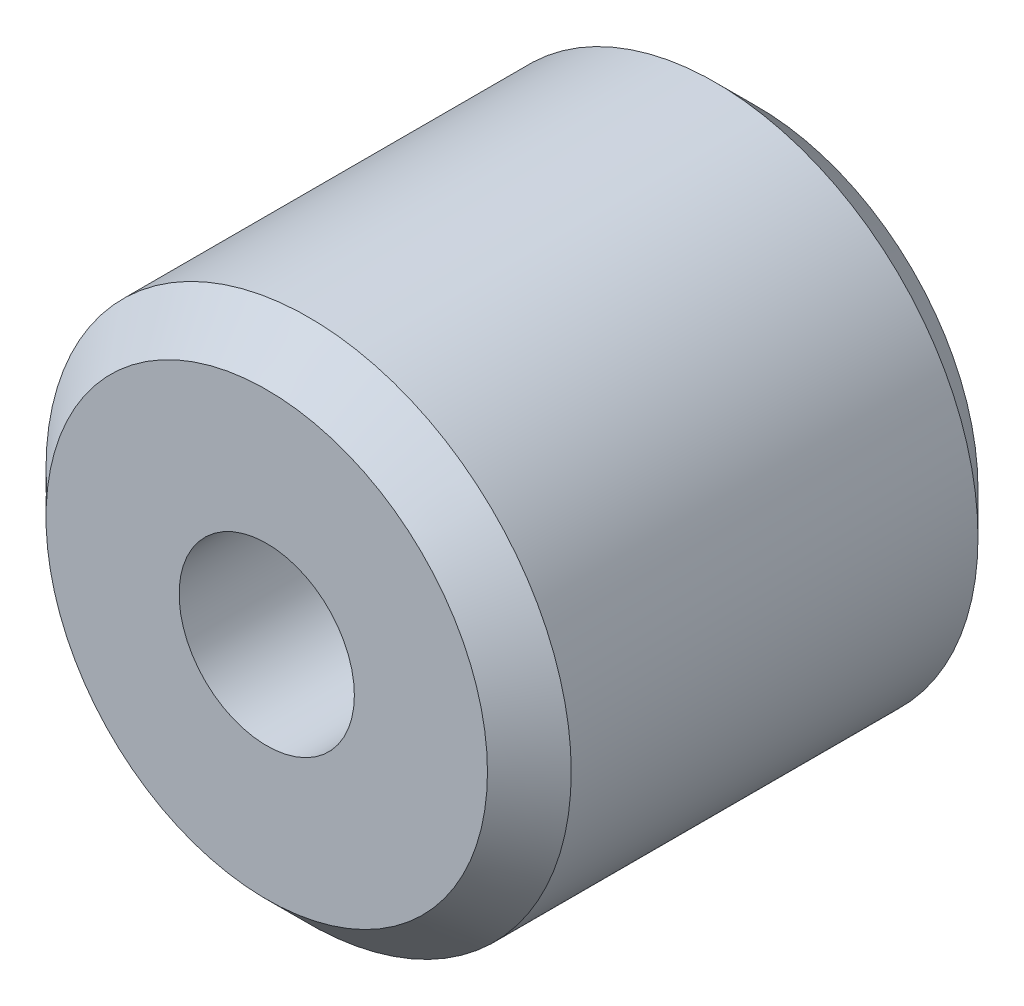
SolidWorks part; units mm, degrees
ref_plane "Front Plane" through (0, 0, 0) normal (0, 0, 1) x (1, 0, 0)
ref_plane "Top Plane" through (0, 0, 0) normal (0, 1, 0) x (1, 0, 0)
ref_plane "Right Plane" through (0, 0, 0) normal (1, 0, 0) x (0, 0, -1)
sketch "Sketch1" plane through (0, 0, 0) normal (1, 0, 0) x (0, 0, -1)
  line L0 (-3.69, 4.765) -> (-4.45, 4.005)
  line L1 (-3.69, 4.765) -> (3.69, 4.765)
  line L3 (4.45, 4.005) -> (3.69, 4.765)
  line L4 (-12.5006, 0) -> (13.4178, 0) construction
  line L5 (-4.45, 4.005) -> (-4.45, 1.59)
  line L6 (-4.45, 1.59) -> (4.45, 1.59)
  line L7 (4.45, 1.59) -> (4.45, 4.005)
  point P0 (0, 4.765)
  point P9 (0, 1.59)
  dimension "D1" = 9.53
  dimension "D2" = 0.76
  dimension "D3" = 45
  dimension "D4" = 3.18
  dimension "D5" = 45
  dimension "D6" = 8.9
revolve "Revolve1" add sketch "Sketch1" angle 360 about L4
